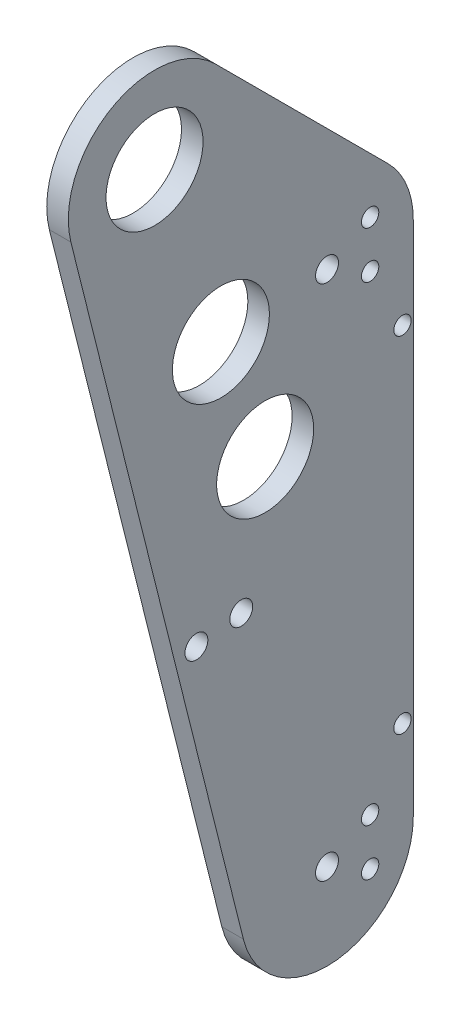
SolidWorks part; units mm, degrees
material "6061-T6 (SS)"
ref_plane "Front Plane" through (0, 0, 0) normal (0, 0, 1) x (1, 0, 0)
ref_plane "Top Plane" through (0, 0, 0) normal (0, 1, 0) x (1, 0, 0)
ref_plane "Right Plane" through (0, 0, 0) normal (1, 0, 0) x (0, 0, -1)
sketch "Sketch1" plane through (0, 0, 0) normal (1, 0, 0) x (0, 0, -1)
  line L0 (0, 0) -> (32.5774, -89.5057) construction
  line L1 (0, 0) -> (0, 78.4081) construction
  line L2 (32.5774, -89.5057) -> (10.2934, -97.6164) construction
  line L3 (50.8, -50.8) -> (50.8, -203.2) construction
  line L4 (73.025, -76.2) -> (50.8, -76.2) construction
  line L5 (0, 0) -> (50.8, -203.2) construction
  line L6 (30.802, -123.2081) -> (12.3208, -127.8284) construction
  point P0 (50.8, -50.8)
  point P1 (50.8, -203.2)
  point P2 (0, 0)
  point P6 (19.5465, -53.7034)
  point P8 (25.5354, -125.8564)
  point P9 (32.5774, -89.5057)
  point P15 (73.025, -177.8)
  dimension "D1" = 152.4
  dimension "D2" = 50.8
  dimension "D3" = 50.8
  dimension "D4" = 20
  dimension "D5" = 38.1
  dimension "D6" = 57.15
  dimension "D7" = 19.05
  dimension "D8" = 31.75
  dimension "D9" = 22.225
  dimension "D10" = 25.4
  dimension "D11" = 101.6
  dimension "D12" = 19.05
  dimension "D13" = 127
sketch "Sketch2" plane through (0, 0, 0) normal (1, 0, 0) x (0, 0, -1)
  line L0 (68.7605, -32.8395) -> (17.9605, 17.9605)
  line L1 (-24.6416, -6.1604) -> (26.1584, -209.3604)
  line L2 (76.2, -203.2) -> (76.2, -50.8)
  arc A0 (17.9605, 17.9605) -> (-24.6416, -6.1604) centre (0, 0) ccw
  arc A1 (76.2, -50.8) -> (68.7605, -32.8395) centre (50.8, -50.8) ccw
  arc A2 (26.1584, -209.3604) -> (76.2, -203.2) centre (50.8, -203.2) ccw
  dimension "D1" = 25.4
extrude "Boss-Extrude1" add sketch "Sketch2" along normal blind 6.35
hole_wizard "1 (1) Diameter Hole1" positions "Sketch3" profile "Sketch4" hole size "1" standard "ANSI Inch" end condition through all
sketch "Sketch3" plane through (6.35, 0, 0) normal (1, 0, 0) x (0, 0, -1)
  point P0 (0, 0)
  point P3 (19.5465, -53.7034)
  point P5 (32.5774, -89.5057)
sketch "Sketch4" plane through (6.35, 0, 0) normal (0, 1, 0) x (0, 0, -1)
  line L0 (0, 0) -> (0, 6.35)
  line L1 (0, 6.35) -> (14.2875, 6.35)
  line L2 (14.2875, 6.35) -> (14.2875, 0)
  line L5 (14.2875, 0) -> (0, 0)
  line L11 (0, -6.35) -> (0, 107.95) construction
  dimension "Thru Hole Dia." = 28.575
  dimension "Thru Hole Depth" = 6.35
hole_wizard "1/4 Clearance Hole1" positions "Sketch7" profile "Sketch8" hole size "1/4" standard "ANSI Inch" end condition through all
sketch "Sketch7" plane through (6.35, 0, 0) normal (1, 0, 0) x (0, 0, -1)
  point P12 (50.8, -50.8)
  point P15 (50.8, -203.2)
  point P18 (12.3208, -127.8284)
sketch "Sketch8" plane through (6.35, -50.8, -50.8) normal (0, 1, 0) x (0, 0, -1)
  line L0 (0, 0) -> (0, 6.35)
  line L1 (0, 6.35) -> (3.3782, 6.35)
  line L2 (3.3782, 6.35) -> (3.3782, 0)
  line L5 (3.3782, 0) -> (0, 0)
  line L11 (0, -6.35) -> (0, 107.95) construction
  dimension "Thru Hole Dia." = 6.7564
  dimension "Thru Hole Depth" = 6.35
hole_wizard "1/4-20 Tapped Hole1" positions "Sketch9" profile "Sketch10" tap size "1/4-20" standard "ANSI Inch" end condition through all
sketch "Sketch9" plane through (0, 0, 0) normal (-1, 0, 0) x (0, 0, 1)
  line L0 (-63.5, -196.2912) -> (-63.5, -210.1088) construction
  line L4 (-63.5, -43.8912) -> (-63.5, -57.7088) construction
  point P0 (-63.5, -57.7088)
  point P2 (-63.5, -43.8912)
  point P4 (-63.5, -210.1088)
  point P6 (-63.5, -196.2912)
  point P43 (-63.5, -203.2)
  point P45 (-63.5, -50.8)
  dimension "D1" = 13.8176
  dimension "D2" = 13.8176
  dimension "D3" = 12.7
  dimension "D4" = 12.7
sketch "Sketch10" plane through (0, -57.7088, -63.5) normal (0, 1, 0) x (0, 0, 1)
  line L0 (0, 0) -> (0, 6.35)
  line L1 (0, 6.35) -> (2.5527, 6.35)
  line L2 (2.5527, 6.35) -> (2.5527, 0)
  line L5 (2.5527, 0) -> (0, 0)
  line L11 (0, -6.35) -> (0, 107.95) construction
  dimension "Thru Tap Drill Dia." = 5.1054
  dimension "Thru Tap Drill Depth" = 6.35
cosmetic thread "Hole Thread1"
cosmetic thread "Hole Thread2"
cosmetic thread "Hole Thread3"
cosmetic thread "Hole Thread4"
hole_wizard "1/4 Clearance Hole2" positions "Sketch11" profile "Sketch12" hole size "1/4" standard "ANSI Inch" end condition through all
sketch "Sketch11" plane through (0, 0, 0) normal (-1, 0, 0) x (0, 0, 1)
  point P0 (-25.5354, -125.8564)
sketch "Sketch12" plane through (0, -125.8564, -25.5354) normal (0, 1, 0) x (0, 0, 1)
  line L0 (0, 0) -> (0, 6.35)
  line L1 (0, 6.35) -> (3.3782, 6.35)
  line L2 (3.3782, 6.35) -> (3.3782, 0)
  line L5 (3.3782, 0) -> (0, 0)
  line L11 (0, -6.35) -> (0, 107.95) construction
  dimension "Thru Hole Dia." = 6.7564
  dimension "Thru Hole Depth" = 6.35
hole_wizard "#10 Clearance Hole1" positions "Sketch13" profile "Sketch14" hole size "#10" standard "ANSI Inch" end condition through all
sketch "Sketch13" plane through (0, 0, 0) normal (-1, 0, 0) x (0, 0, 1)
  point P0 (-73.025, -76.2)
  point P3 (-73.025, -177.8)
sketch "Sketch14" plane through (0, -76.2, -73.025) normal (0, 1, 0) x (0, 0, 1)
  line L0 (0, 0) -> (0, 6.35)
  line L1 (0, 6.35) -> (2.5527, 6.35)
  line L2 (2.5527, 6.35) -> (2.5527, 0)
  line L5 (2.5527, 0) -> (0, 0)
  line L11 (0, -6.35) -> (0, 107.95) construction
  dimension "Thru Hole Dia." = 5.1054
  dimension "Thru Hole Depth" = 6.35
